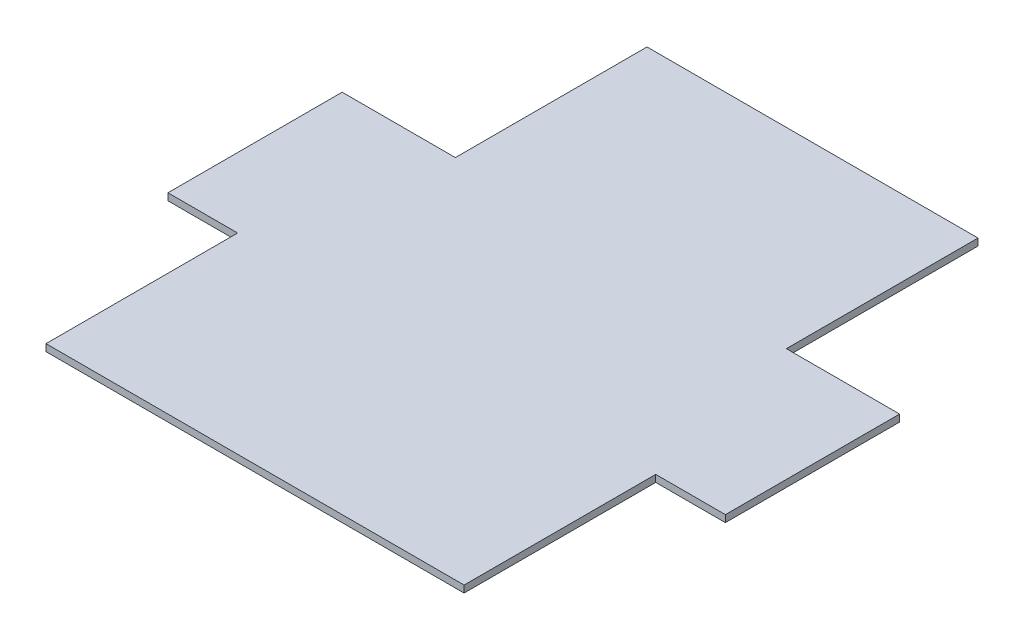
SolidWorks part; units mm, degrees
material "Nylon 6/10"
ref_plane "Front Plane" through (0, 0, 0) normal (0, 0, 1) x (1, 0, 0)
ref_plane "Top Plane" through (0, 0, 0) normal (0, 1, 0) x (1, 0, 0)
ref_plane "Right Plane" through (0, 0, 0) normal (1, 0, 0) x (0, 0, -1)
sketch "Sketch1" plane through (0, 0, 0) normal (0, 1, 0) x (1, 0, 0)
  line L1 (-47.5, 80) -> (47.5, 80)
  line L2 (-47.5, 80) -> (-47.5, 25)
  line L3 (-60, -80) -> (60, -80)
  line L4 (47.5, 80) -> (47.5, 25)
  line L6 (-80, 25) -> (-47.5, 25)
  line L7 (-80, 25) -> (-80, -25)
  line L8 (-80, -25) -> (-60, -25)
  line L9 (80, 25) -> (80, -25)
  line L10 (60, -25) -> (80, -25)
  line L11 (47.5, 25) -> (80, 25)
  line L12 (-60, -25) -> (-60, -80)
  line L13 (60, -25) -> (60, -80)
  point P4 (0, 80)
  dimension "D1" = 160
  dimension "D2" = 95
  dimension "D3" = 160
  dimension "D4" = 50
  dimension "D5" = 55
  dimension "D6" = 80
  dimension "D7" = 120
extrude "Extrude1" add sketch "Sketch1" along normal blind 2
